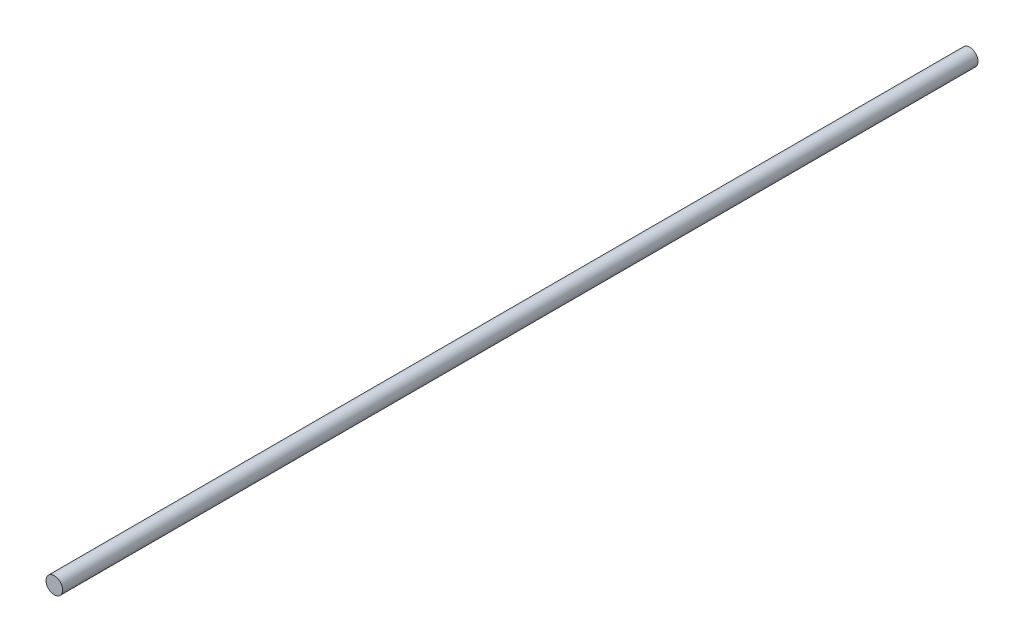
SolidWorks part; units mm, degrees
ref_plane "Plan de face" through (0, 0, 0) normal (0, 0, 1) x (1, 0, 0)
ref_plane "Plan de dessus" through (0, 0, 0) normal (0, 1, 0) x (1, 0, 0)
ref_plane "Plan de droite" through (0, 0, 0) normal (1, 0, 0) x (0, 0, -1)
sketch "Esquisse1" plane through (0, 0, 0) normal (0, 0, 1) x (1, 0, 0)
  circle A0 centre (0, 0) radius 2.45
  dimension "D1" = 4.9
extrude "Boss.-Extru.1" add sketch "Esquisse1" along normal blind 270 contours A0
